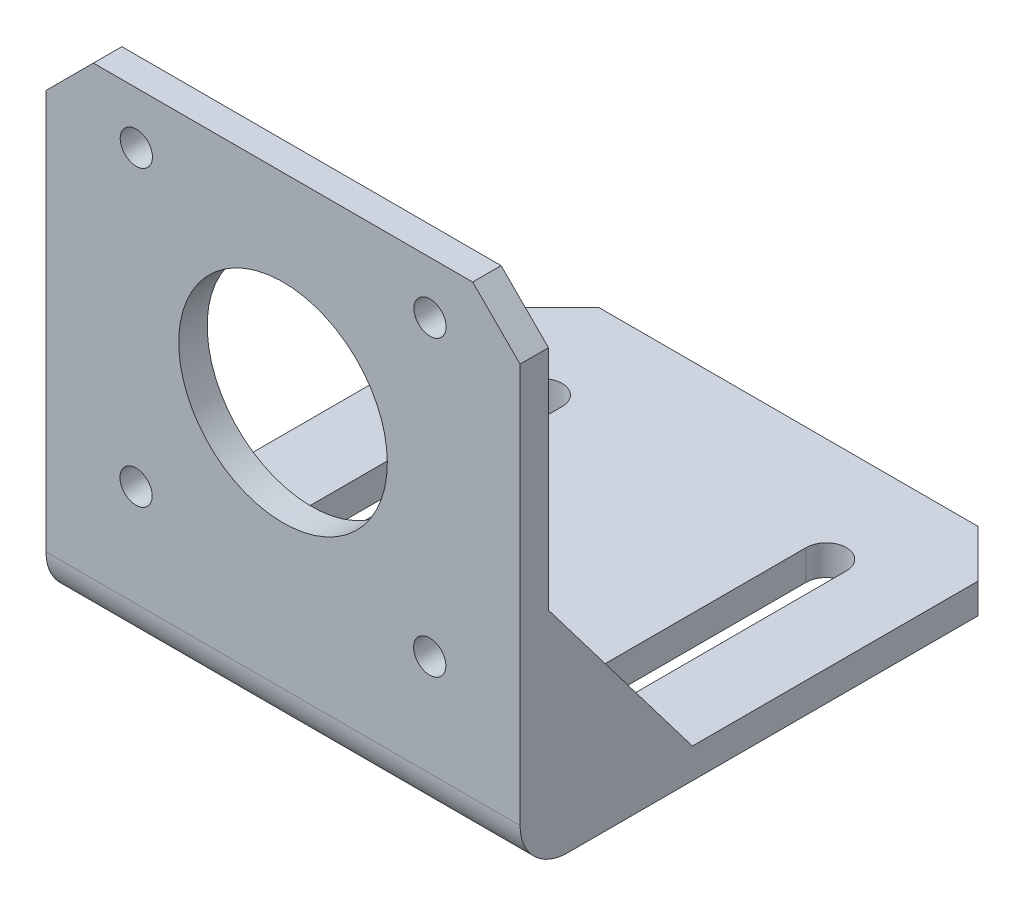
SolidWorks part; units mm, degrees
ref_plane "Front Plane" through (0, 0, 0) normal (0, 0, 1) x (1, 0, 0)
ref_plane "Top Plane" through (0, 0, 0) normal (0, 1, 0) x (1, 0, 0)
ref_plane "Right Plane" through (0, 0, 0) normal (1, 0, 0) x (0, 0, -1)
sketch "Sketch1" plane through (0, 0, 0) normal (0, 1, 0) x (1, 0, 0)
  line L1 (0, 0) -> (50, 0)
  line L2 (0, 0) -> (0, 53.3)
  line L3 (0, 53.3) -> (50, 53.3)
  line L4 (50, 0) -> (50, 53.3)
  dimension "D1" = 50
  dimension "D2" = 53.3
extrude "Boss-Extrude1" add sketch "Sketch1" along normal blind 3.175
sketch "Sketch2" plane through (0, 3.175, 0) normal (0, 1, 0) x (1, 0, 0)
  line L0 (50, 0) -> (50, 53.3) construction
  line L1 (0, 0) -> (50, 0)
  line L2 (0, 0) -> (0, 3)
  line L3 (0, 3) -> (50, 3)
  line L4 (50, 0) -> (50, 3)
  dimension "D1" = 3
extrude "Boss-Extrude2" add sketch "Sketch2" along normal blind 48.97
sketch "Sketch3" plane through (0, 3.175, 0) normal (0, 1, 0) x (1, 0, 0)
  line L1 (0, 3) -> (3.175, 3)
  line L2 (0, 3) -> (0, 18)
  line L3 (0, 18) -> (3.175, 18)
  line L4 (3.175, 3) -> (3.175, 18)
  line L5 (50, 3) -> (46.825, 3)
  line L6 (50, 3) -> (50, 18.175)
  line L7 (50, 18.175) -> (46.825, 18.175)
  line L8 (46.825, 3) -> (46.825, 18.175)
  dimension "D1" = 3.175
  dimension "D2" = 15
  dimension "D3" = 3.175
extrude "Boss-Extrude3" add sketch "Sketch3" along normal blind 20
sketch "Sketch4" plane through (50, 0, 0) normal (1, 0, 0) x (0, 0, -1)
  line L0 (18.175, 3.175) -> (3, 23.175)
  line L1 (3, 23.175) -> (18.175, 23.175)
  line L2 (18.175, 23.175) -> (18.175, 3.175)
extrude "Cut-Extrude1" cut sketch "Sketch4" against normal blind 65
sketch "Sketch5" plane through (0, 0, 0) normal (0, 0, 1) x (1, 0, 0)
  line L0 (25, 52.145) -> (25, 31.145) construction
  line L1 (0, 52.145) -> (50, 52.145) construction
  line L2 (25, 31.145) -> (40.502, 31.145) construction
  line L3 (40.502, 31.145) -> (40.502, 46.647) construction
  line L4 (50, 52.145) -> (0, 52.145) construction
  circle A0 centre (25, 31.145) radius 11
  circle A1 centre (40.502, 46.647) radius 1.7
  circle A2 centre (9.528, 46.677) radius 1.7
  circle A3 centre (9.498, 15.703) radius 1.7
  circle A4 centre (40.472, 15.673) radius 1.7
  point P17 (25, 31.175)
  dimension "D1" = 22
  dimension "D4" = 4
  dimension "D2" = 15.502
  dimension "D3" = 15.502
  dimension "D5" = 21
extrude "Cut-Extrude2" cut sketch "Sketch5" against normal blind 65
sketch "Sketch6" plane through (0, 3.175, 0) normal (0, 1, 0) x (1, 0, 0)
  line L0 (25, 53.3) -> (40, 53.3) construction
  line L1 (50, 53.3) -> (0, 53.3) construction
  line L2 (25, 53.3) -> (10, 53.3) construction
  line L3 (40, 53.3) -> (40, 42.3) construction
  line L4 (10, 53.3) -> (10, 42.3) construction
  line L5 (40, 42.3) -> (40, 12.3) construction
  line L6 (10, 42.3) -> (10, 12.3) construction
  line L7 (37.875, 42.3) -> (37.875, 12.3)
  line L8 (7.875, 42.3) -> (7.875, 12.3)
  line L9 (42.125, 42.3) -> (42.125, 12.3)
  line L10 (12.125, 42.3) -> (12.125, 12.3)
  circle A0 centre (40, 12.3) radius 2.125
  arc A1 (42.125, 42.3) -> (40, 40.175) centre (40, 42.3) ccw
  arc A2 (10, 14.425) -> (12.125, 12.3) centre (10, 12.3) ccw
  circle A3 centre (10, 42.3) radius 2.125
  dimension "D1" = 11
  dimension "D2" = 30
  dimension "D3" = 11
  dimension "D4" = 30
  dimension "D5" = 2.125
  dimension "D6" = 2.125
extrude "Cut-Extrude3" cut sketch "Sketch6" against normal blind 65
chamfer "Chamfer1" distance 5 angle 45 4 edges at (0, 1.5875, -53.3) (50, 1.5875, -53.3) (0, 52.145, -1.5) (50, 52.145, -1.5)
fillet "Fillet1" radius 5 2 edges at (25, 0, 0)
